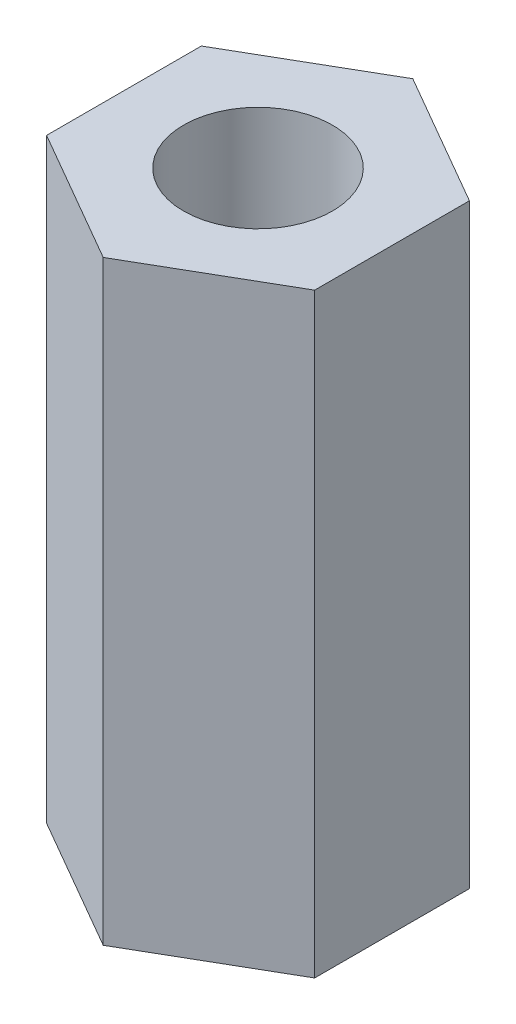
SolidWorks part; units mm, degrees
ref_plane "前视基准面" through (0, 0, 0) normal (0, 0, 1) x (1, 0, 0)
ref_plane "上视基准面" through (0, 0, 0) normal (0, 1, 0) x (1, 0, 0)
ref_plane "右视基准面" through (0, 0, 0) normal (1, 0, 0) x (0, 0, -1)
sketch "草图1" plane through (0, 0, 0) normal (0, 1, 0) x (1, 0, 0)
  line L1 (0, -2.5981) -> (2.25, -1.299)
  line L2 (2.25, -1.299) -> (2.25, 1.299)
  line L3 (2.25, 1.299) -> (0, 2.5981)
  line L4 (0, 2.5981) -> (-2.25, 1.299)
  line L5 (-2.25, 1.299) -> (-2.25, -1.299)
  line L6 (-2.25, -1.299) -> (0, -2.5981)
  circle A0 centre (0, 0) radius 2.25 construction
  dimension "D1" = 4.5
extrude "凸台-拉伸1" add sketch "草图1" along normal mid plane 10
sketch "草图2" plane through (0, 5, 0) normal (0, 1, 0) x (1, 0, 0)
  circle A0 centre (0, 0) radius 1.25
  dimension "D1" = 2.5
extrude "切除-拉伸1" cut sketch "草图2" against normal blind 5
